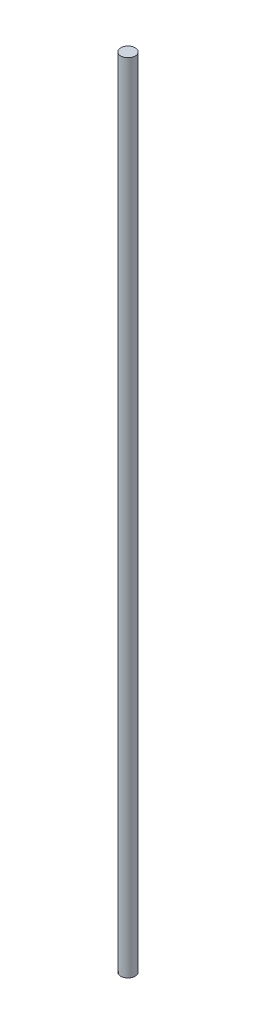
SolidWorks part; units mm, degrees
ref_plane "Plano frontal" through (0, 0, 0) normal (0, 0, 1) x (1, 0, 0)
ref_plane "Plano superior" through (0, 0, 0) normal (0, 1, 0) x (1, 0, 0)
ref_plane "Plano direito" through (0, 0, 0) normal (1, 0, 0) x (0, 0, -1)
sketch "Esboço1" plane through (0, 0, 0) normal (0, 1, 0) x (1, 0, 0)
  circle A0 centre (0, 0) radius 4
  dimension "D1" = 8
extrude "Ressalto-extrusão1" add sketch "Esboço1" along normal mid plane 443
